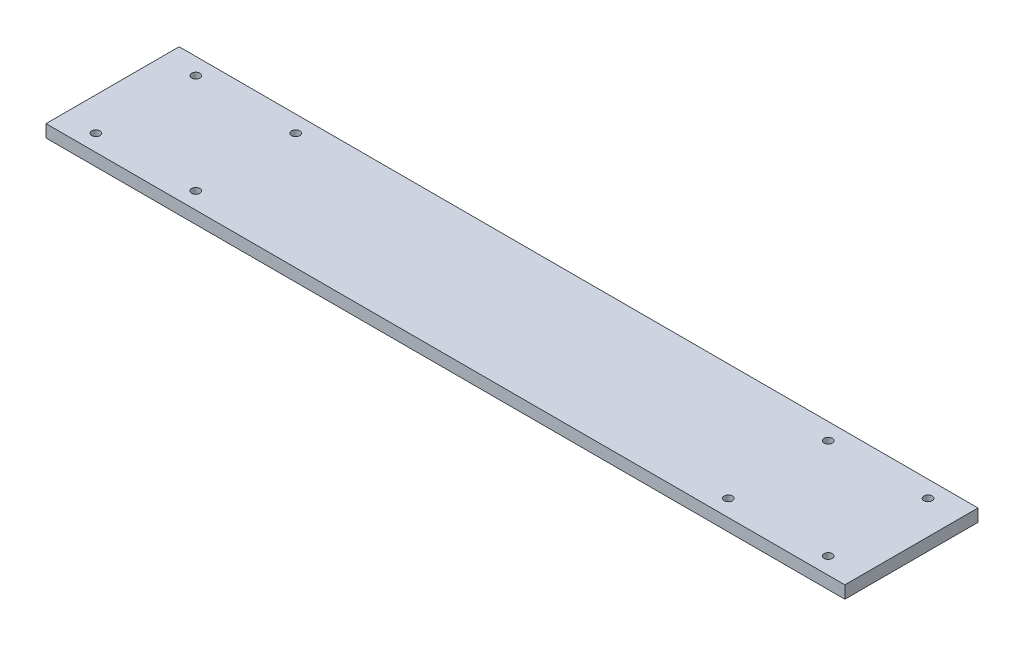
SolidWorks part; units mm, degrees
material "AISI 304"
ref_plane "Front Plane" through (0, 0, 0) normal (0, 0, 1) x (1, 0, 0)
ref_plane "Top Plane" through (0, 0, 0) normal (0, 1, 0) x (1, 0, 0)
ref_plane "Right Plane" through (0, 0, 0) normal (1, 0, 0) x (0, 0, -1)
sketch "Sketch1" plane through (0, 0, 0) normal (0, 1, 0) x (1, 0, 0)
  line L1 (-304.8, -50.8) -> (304.8, -50.8)
  line L2 (-304.8, -50.8) -> (-304.8, 50.8)
  line L3 (-304.8, 50.8) -> (304.8, 50.8)
  line L4 (304.8, -50.8) -> (304.8, 50.8)
  line L5 (-304.8, -50.8) -> (304.8, 50.8) construction
  line L6 (-304.8, 50.8) -> (304.8, -50.8) construction
  point P0 (0, 0)
  dimension "D1" = 609.6
  dimension "D2" = 101.6
extrude "Boss-Extrude1" add sketch "Sketch1" along normal blind 9.525
hole_wizard "1/4 (0.25) Diameter Hole1" positions "Sketch4" profile "Sketch3" hole size "1/4" standard "ANSI Inch" end condition through all
sketch "Sketch4" plane through (0, 9.525, 0) normal (0, 1, 0) x (1, 0, 0)
  line L0 (304.8, -50.8) -> (304.8, 50.8) construction
  line L1 (-304.8, -50.8) -> (304.8, -50.8) construction
  line L3 (-304.8, 50.8) -> (-304.8, -50.8) construction
  point P0 (279.4, -38.1)
  point P2 (279.4, 38.1)
  point P4 (203.2, 38.1)
  point P6 (203.2, -38.1)
  point P8 (-203.2, -38.1)
  point P10 (-279.4, -38.1)
  point P12 (-279.4, 38.1)
  point P14 (-203.2, 38.1)
  dimension "D1" = 76.2
  dimension "D2" = 25.4
  dimension "D3" = 76.2
  dimension "D4" = 12.7
  dimension "D5" = 76.2
  dimension "D6" = 25.4
sketch "Sketch3" plane through (279.4, 9.525, 38.1) normal (1, 0, 0) x (0, 0, 1)
  line L0 (0, 0) -> (0, 9.525)
  line L1 (0, 9.525) -> (3.175, 9.525)
  line L2 (3.175, 9.525) -> (3.175, 0)
  line L5 (3.175, 0) -> (0, 0)
  line L11 (0, -6.35) -> (0, 107.95) construction
  dimension "Thru Hole Dia." = 6.35
  dimension "Thru Hole Depth" = 9.525
